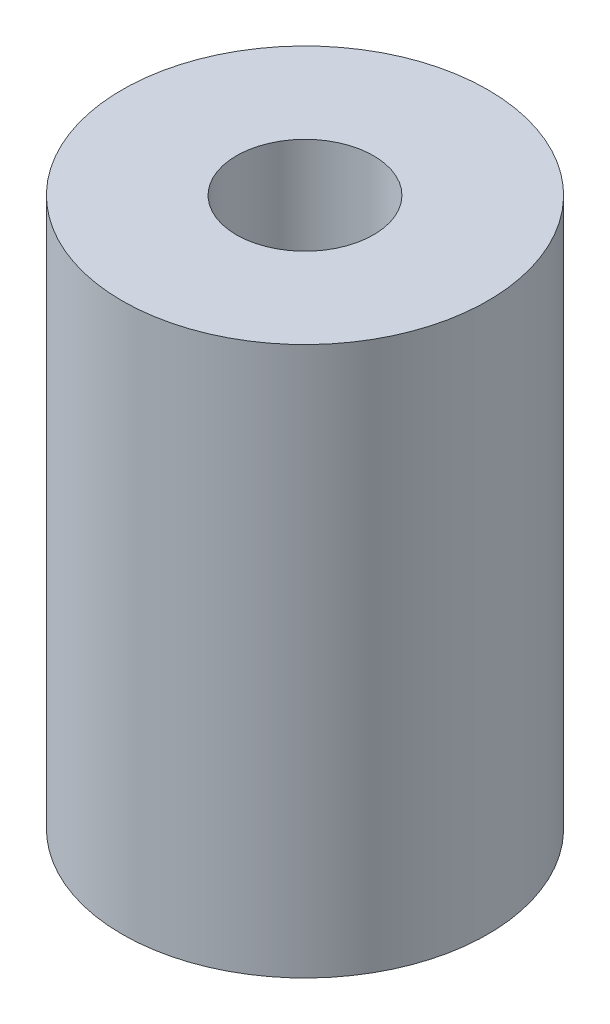
SolidWorks part; units mm, degrees
ref_plane "Front Plane" through (0, 0, 0) normal (0, 0, 1) x (1, 0, 0)
ref_plane "Top Plane" through (0, 0, 0) normal (0, 1, 0) x (1, 0, 0)
ref_plane "Right Plane" through (0, 0, 0) normal (1, 0, 0) x (0, 0, -1)
sketch "Esquisse1" plane through (0, 0, 0) normal (0, 1, 0) x (1, 0, 0)
  circle A0 centre (0, 0) radius 1.5
  circle A1 centre (0, 0) radius 4
  dimension "D1" = 8
  dimension "D2" = 3
extrude "Boss.-Extru.1" add sketch "Esquisse1" along normal blind 12
